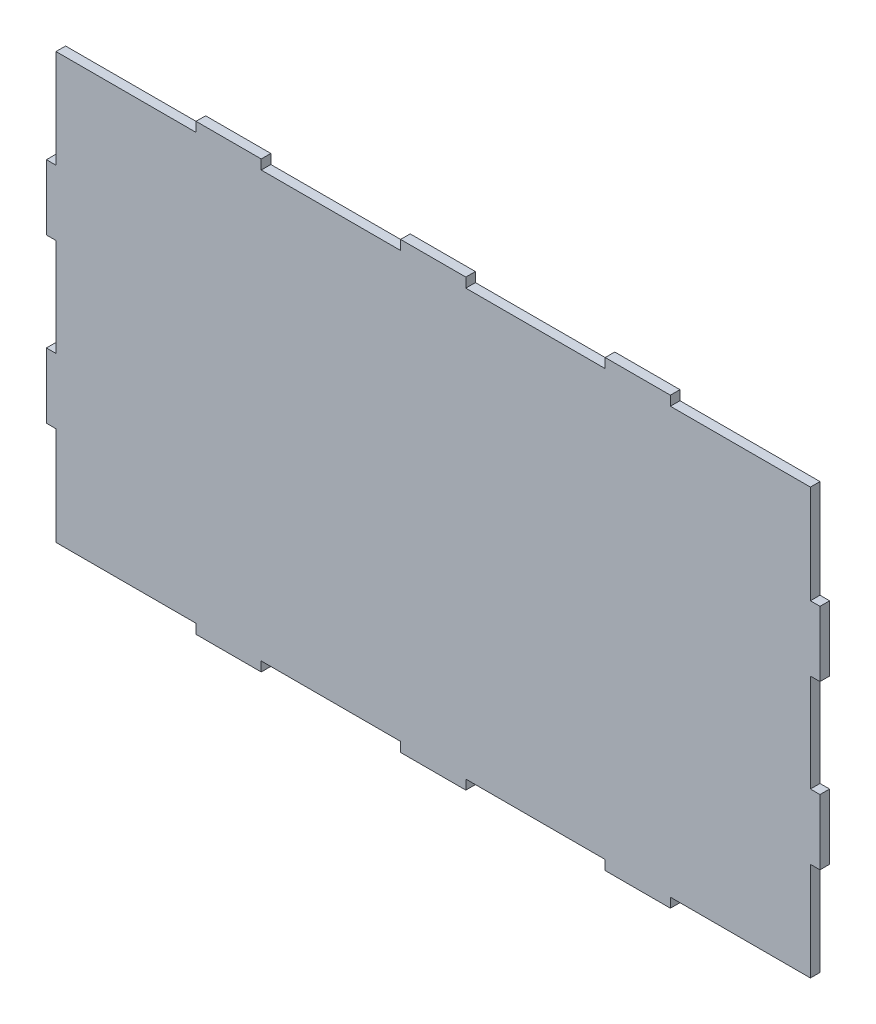
SolidWorks part; units mm, degrees
ref_plane "Спереди" through (0, 0, 0) normal (0, 0, 1) x (1, 0, 0)
ref_plane "Сверху" through (0, 0, 0) normal (0, 1, 0) x (1, 0, 0)
ref_plane "Справа" through (0, 0, 0) normal (1, 0, 0) x (0, 0, -1)
sketch "Эскиз4" plane through (0, 0, 0) normal (0, 0, 1) x (1, 0, 0)
  line L0 (0, 133) -> (0, 102.2)
  line L1 (0, 0) -> (43.8, 0)
  line L2 (0, 0) -> (0, 30.8)
  line L3 (0, 133) -> (43.8, 133)
  line L4 (236, 0) -> (236, 30.8)
  line L5 (0, 102.2) -> (-3, 102.2)
  line L6 (-3, 102.2) -> (-3, 81.8)
  line L7 (-3, 81.8) -> (0, 81.8)
  line L8 (0, 81.8) -> (0, 60.66)
  line L9 (0, 51.2) -> (-3, 51.2)
  line L10 (-3, 51.2) -> (-3, 30.8)
  line L11 (-3, 30.8) -> (0, 30.8)
  line L12 (236, 133) -> (236, 102.2)
  line L13 (192.2, -3) -> (192.2, 0)
  line L14 (171.8, 0) -> (171.8, -3)
  line L15 (171.8, -3) -> (192.2, -3)
  line L16 (128.2, -3) -> (128.2, 0)
  line L17 (107.8, -3) -> (128.2, -3)
  line L18 (107.8, 0) -> (107.8, -3)
  line L19 (0, 133) -> (43.8, 133)
  line L20 (43.8, 133) -> (43.8, 136)
  line L21 (43.8, 136) -> (64.2, 136)
  line L22 (64.2, 136) -> (64.2, 133)
  line L23 (107.8, 136) -> (128.2, 136)
  line L24 (107.8, 133) -> (107.8, 136)
  line L25 (128.2, 136) -> (128.2, 133)
  line L26 (171.8, 136) -> (192.2, 136)
  line L27 (171.8, 133) -> (171.8, 136)
  line L28 (192.2, 136) -> (192.2, 133)
  line L29 (0, 66.5) -> (284.8246, 66.5) construction
  line L30 (64.2, -3) -> (64.2, 0)
  line L31 (43.8, 0) -> (43.8, -3)
  line L32 (43.8, -3) -> (64.2, -3)
  line L33 (118, 133) -> (118, -66.2582) construction
  line L34 (239, 30.8) -> (236, 30.8)
  line L35 (236, 51.2) -> (239, 51.2)
  line L36 (239, 51.2) -> (239, 30.8)
  line L37 (239, 81.8) -> (236, 81.8)
  line L38 (239, 102.2) -> (239, 81.8)
  line L39 (236, 102.2) -> (239, 102.2)
  line L40 (64.2, 133) -> (107.8, 133)
  line L41 (128.2, 133) -> (171.8, 133)
  line L42 (192.2, 133) -> (236, 133)
  line L43 (236, 102.2) -> (236, 133)
  line L44 (236, 51.2) -> (236, 81.8)
  line L45 (192.2, 0) -> (236, 0)
  line L46 (128.2, 0) -> (171.8, 0)
  line L47 (64.2, 0) -> (107.8, 0)
  line L48 (0, 51.2) -> (0, 81.8)
  line L49 (0, 102.2) -> (0, 133)
  dimension "D4" = 20.4
  dimension "D1" = 133
  dimension "D2" = 236
  dimension "D3" = 2
  dimension "D5" = 3
  dimension "D6" = 3
  dimension "D8" = 20.4
  dimension "D9" = 3
  dimension "D10" = 30.8
  dimension "D11" = 43.8
extrude "Бобышка-Вытянуть3" add sketch "Эскиз4" along normal blind 3 contours L48 L9 L10 L11 L2 L1 L31 L32 L30 L47 L18 L17 L16 L46 L14 L15 L13 L45 L4 L34 L36 L35 L44 L37 L38 L39 L12 L42 L28 L26 L27 L41 L25 L23 L24 L40 L22 L21 L20 L3 L0 L5 L6 L7 L8
